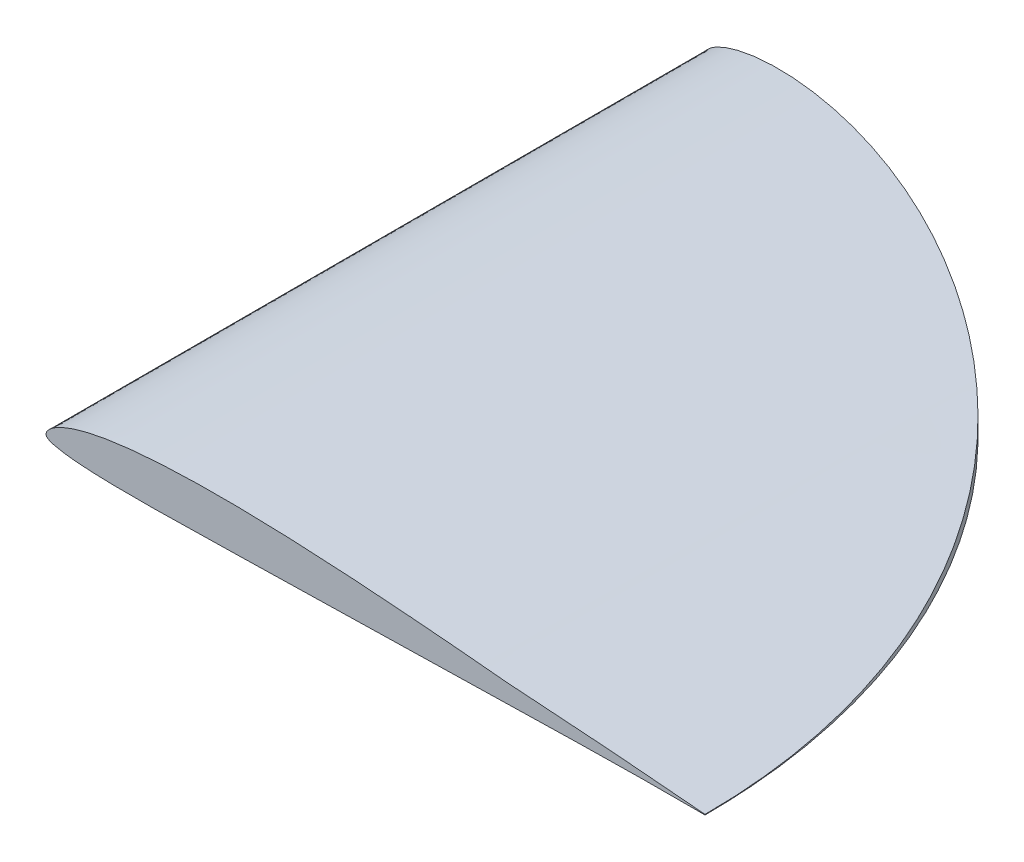
SolidWorks part; units mm, degrees
ref_plane "Front Plane" through (0, 0, 0) normal (0, 0, 1) x (1, 0, 0)
ref_plane "Top Plane" through (0, 0, 0) normal (0, 1, 0) x (1, 0, 0)
ref_plane "Right Plane" through (0, 0, 0) normal (1, 0, 0) x (0, 0, -1)
curve "Curve1"
  spline degree 3 poles (25.4, 0.0107, 0) (25.3506, 0.0152, 0) (25.2009, 0.0289, 0) (24.9376, 0.0531, 0) (24.6076, 0.082, 0) (24.2616, 0.1124, 0) (23.9125, 0.1431, 0) (23.5625, 0.1725, 0) (23.212, 0.2019, 0) (22.8613, 0.2307, 0) (22.5105, 0.2591, 0) (22.1596, 0.2869, 0) (21.8089, 0.314, 0) (21.4582, 0.3409, 0) (21.1077, 0.367, 0) (20.7573, 0.3928, 0) (20.407, 0.4182, 0) (20.0568, 0.4428, 0) (19.7068, 0.4673, 0) (19.3568, 0.4911, 0) (19.0069, 0.5145, 0) (18.6571, 0.5374, 0) (18.3335, 0.5583, 0) (18.0818, 0.5739, 0) (17.9246, 0.5843, 0) (17.8356, 0.5888, 0) (17.7472, 0.5983, 0) (17.5613, 0.6156, 0) (17.278, 0.6431, 0) (16.98, 0.6709, 0) (16.7137, 0.6956, 0) (16.4751, 0.7176, 0) (16.176, 0.7447, 0) (15.8267, 0.776, 0) (15.4701, 0.8073, 0) (15.1145, 0.838, 0) (14.7793, 0.8663, 0) (14.4495, 0.8936, 0) (14.1621, 0.9169, 0) (13.925, 0.9358, 0) (13.6642, 0.9563, 0) (13.3619, 0.9794, 0) (13.0103, 1.0056, 0) (12.659, 1.031, 0) (12.3077, 1.0554, 0) (11.9565, 1.0789, 0) (11.6054, 1.1014, 0) (11.2544, 1.1228, 0) (10.9034, 1.1432, 0) (10.5525, 1.1624, 0) (10.2016, 1.1803, 0) (9.8507, 1.197, 0) (9.5, 1.2123, 0) (9.1492, 1.2263, 0) (8.7986, 1.2386, 0) (8.448, 1.2494, 0) (8.0977, 1.2585, 0) (7.7474, 1.2658, 0) (7.3974, 1.2711, 0) (7.0475, 1.2745, 0) (6.6979, 1.2756, 0) (6.3485, 1.2744, 0) (5.9995, 1.2706, 0) (5.6509, 1.2642, 0) (5.3028, 1.2548, 0) (4.9554, 1.2422, 0) (4.6087, 1.2261, 0) (4.2629, 1.2062, 0) (3.9183, 1.1823, 0) (3.5751, 1.1536, 0) (3.2336, 1.12, 0) (2.8944, 1.0807, 0) (2.5581, 1.0351, 0) (2.2254, 0.9824, 0) (1.8975, 0.9214, 0) (1.5762, 0.8511, 0) (1.2643, 0.7698, 0) (0.9677, 0.6771, 0) (0.6972, 0.5737, 0) (0.4689, 0.4653, 0) (0.2948, 0.361, 0) (0.1747, 0.2696, 0) (0.0967, 0.1939, 0) (0.0471, 0.1311, 0) (0.0171, 0.0777, 0) (0.0019, 0.0319, 0) (-0.0016, -0.0085, 0) (0.0071, -0.0466, 0) (0.0322, -0.0832, 0) (0.0764, -0.1158, 0) (0.1405, -0.1489, 0) (0.2348, -0.1846, 0) (0.3747, -0.2244, 0) (0.5727, -0.265, 0) (0.8268, -0.3029, 0) (1.1218, -0.3343, 0) (1.4394, -0.3584, 0) (1.7684, -0.3763, 0) (2.1036, -0.389, 0) (2.4428, -0.3976, 0) (2.7846, -0.4031, 0) (3.1285, -0.4061, 0) (3.4739, -0.407, 0) (3.8205, -0.4061, 0) (4.168, -0.4035, 0) (4.5164, -0.3997, 0) (4.8654, -0.3948, 0) (5.2151, -0.389, 0) (5.5654, -0.3825, 0) (5.9165, -0.3755, 0) (6.2684, -0.368, 0) (6.621, -0.3604, 0) (6.9745, -0.3524, 0) (7.3287, -0.3442, 0) (7.6835, -0.336, 0) (8.039, -0.3276, 0) (8.3948, -0.3192, 0) (8.7511, -0.3108, 0) (9.1077, -0.3024, 0) (9.4646, -0.2939, 0) (9.8219, -0.2855, 0) (10.1795, -0.2771, 0) (10.5373, -0.2687, 0) (10.8952, -0.2603, 0) (11.2527, -0.252, 0) (11.6101, -0.2438, 0) (11.9672, -0.2355, 0) (12.3241, -0.2274, 0) (12.6807, -0.2193, 0) (13.0371, -0.2114, 0) (13.3934, -0.2033, 0) (13.6949, -0.1966, 0) (13.9592, -0.1908, 0) (14.1921, -0.1856, 0) (14.4749, -0.1792, 0) (14.7878, -0.1723, 0) (15.131, -0.1647, 0) (15.4754, -0.1569, 0) (15.8234, -0.1492, 0) (16.1349, -0.1423, 0) (16.4075, -0.1363, 0) (16.6379, -0.1313, 0) (16.9029, -0.1255, 0) (17.2072, -0.1189, 0) (17.4885, -0.1128, 0) (17.6791, -0.1088, 0) (17.7715, -0.1068, 0) (17.8501, -0.1053, 0) (18.0096, -0.1018, 0) (18.269, -0.0964, 0) (18.61, -0.0893, 0) (18.9621, -0.082, 0) (19.3141, -0.0749, 0) (19.666, -0.0678, 0) (20.0179, -0.0609, 0) (20.3698, -0.054, 0) (20.7219, -0.0473, 0) (21.074, -0.0408, 0) (21.4262, -0.0348, 0) (21.7784, -0.0292, 0) (22.1308, -0.0242, 0) (22.4832, -0.0197, 0) (22.8357, -0.0157, 0) (23.1883, -0.0125, 0) (23.5408, -0.0098, 0) (23.8935, -0.008, 0) (24.246, -0.0071, 0) (24.5963, -0.007, 0) (24.9308, -0.0084, 0) (25.198, -0.0096, 0) (25.3499, -0.0104, 0) (25.4, -0.0107, 0) knots 0 0 0 0 0.002901 0.008799 0.015478 0.022288 0.029131 0.035985 0.042847 0.049714 0.056581 0.063448 0.070313 0.077171 0.084031 0.090885 0.097737 0.104584 0.111432 0.118275 0.125116 0.131954 0.138793 0.144098 0.146709 0.148014 0.149313 0.151911 0.158945 0.165974 0.169425 0.174599 0.18 0.186998 0.195126 0.200949 0.20789 0.214818 0.220317 0.224762 0.228741 0.235631 0.242503 0.249376 0.256249 0.263115 0.269975 0.276837 0.283698 0.290553 0.297409 0.304262 0.311112 0.317958 0.324805 0.331647 0.338484 0.345319 0.352149 0.358974 0.365797 0.372613 0.37942 0.386225 0.393018 0.399801 0.406576 0.413331 0.420073 0.426793 0.433487 0.440154 0.446776 0.453353 0.459862 0.466294 0.472602 0.478718 0.484477 0.489534 0.493496 0.496331 0.498346 0.499841 0.500999 0.501915 0.502649 0.503345 0.504158 0.505185 0.506526 0.508376 0.511074 0.515031 0.520197 0.526109 0.532386 0.538838 0.545393 0.552019 0.558693 0.565404 0.572145 0.578909 0.585689 0.592488 0.599298 0.60612 0.612956 0.619809 0.626673 0.633554 0.640451 0.647364 0.654291 0.661227 0.668172 0.675126 0.682086 0.689049 0.69602 0.703 0.709987 0.71697 0.723948 0.73092 0.73789 0.744856 0.751814 0.758769 0.765721 0.77267 0.776424 0.78119 0.786305 0.792978 0.79951 0.806399 0.81314 0.819881 0.824633 0.829103 0.833367 0.840145 0.84692 0.849831 0.851305 0.852333 0.85443 0.860642 0.867519 0.87439 0.881257 0.888123 0.894989 0.901857 0.908727 0.915597 0.922469 0.929344 0.936217 0.943092 0.949972 0.956848 0.963729 0.970609 0.97749 0.984361 0.991109 0.997067 1 1 1 1
sketch "Sketch2" plane through (0, 0, 0) normal (0, 0, 1) x (1, 0, 0)
  line L0 (64.7182, -2.4991) -> (64.7182, -2.5635)
  line L1 (127, 0.0536) -> (127, -0.0536)
  line L2 (25.4, 0.0107) -> (25.4, -0.0107)
  line L3 (279.4, 0.1179) -> (279.4, -0.1179)
  line L4 (609.6, 0.2573) -> (609.6, -0.2573)
  spline S1 degree 3 poles (609.6, 0.2573) (608.4153, 0.3652) (604.8219, 0.6927) (598.502, 1.2752) (590.5825, 1.9674) (582.2775, 2.6983) (573.9006, 3.4339) (565.4998, 4.1403) (557.089, 4.8463) (548.6715, 5.5358) (540.2515, 6.218) (531.8311, 6.8852) (523.413, 7.5348) (514.9974, 8.1818) (506.5852, 8.8084) (498.1747, 9.4281) (489.7686, 10.036) (481.3637, 10.627) (472.9627, 11.2149) (464.5629, 11.7866) (456.1664, 12.3471) (447.7708, 12.8983) (440.0032, 13.3997) (433.9644, 13.7741) (430.1915, 14.0231) (428.0555, 14.1319) (425.9338, 14.3593) (421.4712, 14.7735) (414.6712, 15.4343) (407.5204, 16.1015) (401.1285, 16.6942) (395.4014, 17.222) (388.2248, 17.8734) (379.8411, 18.6251) (371.2834, 19.3759) (362.7481, 20.1109) (354.702, 20.791) (346.7874, 21.4473) (339.8916, 22.0057) (334.2002, 22.4585) (327.9397, 22.9514) (320.686, 23.506) (312.248, 24.1341) (303.8155, 24.7432) (292.5775, 25.5244) (281.3407, 26.2607) (270.1062, 26.9482) (261.6823, 27.4364) (250.4535, 28.0507) (239.2258, 28.6059) (227.9988, 29.096) (219.5815, 29.4314) (211.1661, 29.7272) (202.7531, 29.9856) (194.3438, 30.2035) (185.9386, 30.3795) (177.5376, 30.5072) (169.1408, 30.5885) (160.7491, 30.6149) (152.3646, 30.5852) (143.9885, 30.4949) (135.6226, 30.341) (127.2682, 30.115) (118.9286, 29.8125) (110.6079, 29.4273) (102.3088, 28.9496) (94.0382, 28.3746) (85.8017, 27.6874) (77.6067, 26.8808) (69.4667, 25.9361) (61.3935, 24.8424) (53.4108, 23.5771) (45.5411, 22.1146) (37.8288, 20.426) (30.344, 18.4761) (23.2242, 16.2498) (16.7336, 13.7685) (11.2526, 11.1662) (7.0744, 8.6642) (4.192, 6.4716) (2.3207, 4.6541) (1.1306, 3.147) (0.4097, 1.8653) (0.0445, 0.7644) (-0.0394, -0.2051) (0.1701, -1.1192) (0.7717, -1.9972) (1.8329, -2.7786) (3.3717, -3.5735) (5.6341, -4.4311) (8.992, -5.3852) (13.7441, -6.3602) (19.844, -7.2691) (26.9221, -8.0223) (34.5451, -8.6019) (42.4418, -9.0313) (50.4869, -9.3361) (58.6261, -9.543) (66.8307, -9.6749) (75.0831, -9.7467) (83.3728, -9.7692) (91.6908, -9.7458) (100.0329, -9.6848) (108.3931, -9.5935) (116.7701, -9.4746) (125.1618, -9.3356) (133.5708, -9.1799) (141.9971, -9.0125) (150.4416, -8.8321) (158.9043, -8.6491) (167.3869, -8.4567) (175.8879, -8.2608) (187.2521, -7.9967) (198.6327, -7.7272) (210.0269, -7.4583) (218.5851, -7.2569) (227.1506, -7.0539) (235.7244, -6.8527) (244.3077, -6.6496) (252.896, -6.449) (261.4836, -6.2483) (270.0654, -6.0486) (278.6417, -5.8521) (287.2128, -5.6526) (295.7783, -5.4585) (304.3375, -5.264) (312.891, -5.0728) (321.4408, -4.88) (328.6786, -4.7192) (337.1174, -4.5324) (345.4426, -4.3447) (354.9071, -4.135) (363.1446, -3.9522) (371.4102, -3.7664) (379.7615, -3.5814) (387.2366, -3.4158) (393.7811, -3.2715) (399.3097, -3.1512) (405.6693, -3.0117) (412.9735, -2.8543) (419.723, -2.7081) (424.2983, -2.6117) (426.5172, -2.5634) (428.4027, -2.5274) (432.2303, -2.443) (438.4564, -2.3133) (446.6397, -2.1424) (455.0912, -1.9684) (463.5382, -1.7984) (471.983, -1.6281) (480.4288, -1.4625) (488.876, -1.2962) (497.3253, -1.1358) (505.7757, -0.9782) (514.2284, -0.8363) (525.5014, -0.6571) (536.7782, -0.5043) (548.0561, -0.376) (556.518, -0.299) (564.9803, -0.2347) (573.4446, -0.1921) (581.9048, -0.1708) (590.3111, -0.1673) (598.3385, -0.2004) (604.7515, -0.2296) (608.3973, -0.2504) (609.6, -0.2573) knots 0 0 0 0 0.002901 0.008799 0.015478 0.022288 0.029131 0.035985 0.042847 0.049714 0.056581 0.063448 0.070313 0.077171 0.084031 0.090885 0.097737 0.104584 0.111432 0.118275 0.125116 0.131954 0.138793 0.144098 0.146709 0.148014 0.149313 0.151911 0.158945 0.165974 0.169425 0.174599 0.18 0.186998 0.195126 0.200949 0.20789 0.214818 0.220317 0.224762 0.228741 0.235631 0.242503 0.249376 0.256249 0.269975 0.276837 0.283698 0.290553 0.304262 0.311112 0.317958 0.324805 0.331647 0.338484 0.345319 0.352149 0.358974 0.365797 0.372613 0.37942 0.386225 0.393018 0.399801 0.406576 0.413331 0.420073 0.426793 0.433487 0.440154 0.446776 0.453353 0.459862 0.466294 0.472602 0.478718 0.484477 0.489534 0.493496 0.496331 0.498346 0.499841 0.500999 0.501915 0.502649 0.503345 0.504158 0.505185 0.506526 0.508376 0.511074 0.515031 0.520197 0.526109 0.532386 0.538838 0.545393 0.552019 0.558693 0.565404 0.572145 0.578909 0.585689 0.592488 0.599298 0.60612 0.612956 0.619809 0.626673 0.633554 0.640451 0.647364 0.654291 0.668172 0.675126 0.682086 0.689049 0.69602 0.703 0.709987 0.71697 0.723948 0.73092 0.73789 0.744856 0.751814 0.758769 0.765721 0.77267 0.776424 0.786305 0.792978 0.79951 0.806399 0.81314 0.819881 0.824633 0.829103 0.833367 0.840145 0.84692 0.849831 0.851305 0.852333 0.85443 0.860642 0.867519 0.87439 0.881257 0.888123 0.894989 0.901857 0.908727 0.915597 0.922469 0.929344 0.943092 0.949972 0.956848 0.963729 0.970609 0.97749 0.984361 0.991109 0.997067 1 1 1 1
  spline S2 degree 3 poles (127, 0.0536) (126.7532, 0.0761) (126.0046, 0.1443) (124.6879, 0.2657) (123.038, 0.4099) (121.3078, 0.5622) (119.5626, 0.7154) (117.8125, 0.8626) (116.0602, 1.0096) (114.3066, 1.1533) (112.5524, 1.2954) (110.7981, 1.4344) (109.0444, 1.5698) (107.2911, 1.7045) (105.5386, 1.8351) (103.7864, 1.9642) (102.0351, 2.0908) (100.2841, 2.214) (98.5339, 2.3364) (96.7839, 2.4555) (95.0347, 2.5723) (93.2856, 2.6871) (91.6673, 2.7916) (90.4092, 2.8696) (89.6232, 2.9215) (89.1782, 2.9441) (88.7362, 2.9915) (87.8065, 3.0778) (86.3898, 3.2155) (84.9001, 3.3545) (83.5684, 3.478) (82.3753, 3.5879) (80.8802, 3.7236) (79.1336, 3.8802) (77.3507, 4.0366) (75.5725, 4.1898) (73.8963, 4.3315) (72.2474, 4.4682) (70.8107, 4.5845) (69.625, 4.6789) (68.3208, 4.7815) (66.8096, 4.8971) (65.0517, 5.0279) (63.2949, 5.1548) (60.9536, 5.3176) (58.6126, 5.471) (56.2721, 5.6142) (54.5172, 5.7159) (52.1778, 5.8439) (49.8387, 5.9596) (47.4998, 6.0617) (45.7461, 6.1315) (43.9929, 6.1932) (42.2402, 6.247) (40.4883, 6.2924) (38.7372, 6.3291) (36.987, 6.3557) (35.2377, 6.3726) (33.4894, 6.3781) (31.7426, 6.3719) (29.9976, 6.3531) (28.2547, 6.321) (26.5142, 6.274) (24.7768, 6.2109) (23.0433, 6.1307) (21.3143, 6.0312) (19.5913, 5.9114) (17.8753, 5.7682) (16.1681, 5.6002) (14.4722, 5.4034) (12.7903, 5.1755) (11.1272, 4.9119) (9.4877, 4.6072) (7.881, 4.2554) (6.3217, 3.8492) (4.8384, 3.3854) (3.4862, 2.8684) (2.3443, 2.3263) (1.4738, 1.805) (0.8733, 1.3482) (0.4835, 0.9696) (0.2355, 0.6556) (0.0854, 0.3886) (0.0093, 0.1593) (-0.0082, -0.0427) (0.0354, -0.2332) (0.1608, -0.4161) (0.3818, -0.5789) (0.7024, -0.7445) (1.1738, -0.9231) (1.8733, -1.1219) (2.8634, -1.3251) (4.1342, -1.5144) (5.6088, -1.6713) (7.1969, -1.7921) (8.842, -1.8815) (10.5181, -1.945) (12.2138, -1.9881) (13.9231, -2.0156) (15.6423, -2.0306) (17.3693, -2.0352) (19.1023, -2.0304) (20.8402, -2.0177) (22.5819, -1.9987) (24.3271, -1.9739) (26.0754, -1.9449) (27.8272, -1.9125) (29.5827, -1.8776) (31.342, -1.84) (33.1051, -1.8019) (34.8723, -1.7618) (36.6433, -1.721) (39.0109, -1.666) (41.3818, -1.6098) (43.7556, -1.5538) (45.5386, -1.5118) (47.323, -1.4696) (49.1093, -1.4276) (50.8974, -1.3853) (52.6867, -1.3435) (54.4758, -1.3017) (56.2636, -1.2601) (58.0503, -1.2192) (59.836, -1.1776) (61.6205, -1.1372) (63.4036, -1.0967) (65.1856, -1.0568) (66.9668, -1.0167) (68.4747, -0.9832) (70.2328, -0.9443) (71.9672, -0.9051) (73.939, -0.8615) (75.6551, -0.8234) (77.3771, -0.7847) (79.117, -0.7461) (80.6743, -0.7116) (82.0377, -0.6816) (83.1895, -0.6565) (84.5144, -0.6274) (86.0361, -0.5947) (87.4423, -0.5642) (88.3955, -0.5441) (88.8577, -0.534) (89.2506, -0.5265) (90.048, -0.509) (91.3451, -0.4819) (93.0499, -0.4463) (94.8107, -0.4101) (96.5705, -0.3747) (98.3298, -0.3392) (100.0893, -0.3047) (101.8492, -0.27) (103.6094, -0.2366) (105.3699, -0.2038) (107.1309, -0.1742) (109.4795, -0.1369) (111.8288, -0.1051) (114.1784, -0.0783) (115.9413, -0.0623) (117.7042, -0.0489) (119.4676, -0.04) (121.2302, -0.0356) (122.9815, -0.0349) (124.6538, -0.0418) (125.9899, -0.0478) (126.7494, -0.0522) (127, -0.0536) knots 0 0 0 0 0.002901 0.008799 0.015478 0.022288 0.029131 0.035985 0.042847 0.049714 0.056581 0.063448 0.070313 0.077171 0.084031 0.090885 0.097737 0.104584 0.111432 0.118275 0.125116 0.131954 0.138793 0.144098 0.146709 0.148014 0.149313 0.151911 0.158945 0.165974 0.169425 0.174599 0.18 0.186998 0.195126 0.200949 0.20789 0.214818 0.220317 0.224762 0.228741 0.235631 0.242503 0.249376 0.256249 0.269975 0.276837 0.283698 0.290553 0.304262 0.311112 0.317958 0.324805 0.331647 0.338484 0.345319 0.352149 0.358974 0.365797 0.372613 0.37942 0.386225 0.393018 0.399801 0.406576 0.413331 0.420073 0.426793 0.433487 0.440154 0.446776 0.453353 0.459862 0.466294 0.472602 0.478718 0.484477 0.489534 0.493496 0.496331 0.498346 0.499841 0.500999 0.501915 0.502649 0.503345 0.504158 0.505185 0.506526 0.508376 0.511074 0.515031 0.520197 0.526109 0.532386 0.538838 0.545393 0.552019 0.558693 0.565404 0.572145 0.578909 0.585689 0.592488 0.599298 0.60612 0.612956 0.619809 0.626673 0.633554 0.640451 0.647364 0.654291 0.668172 0.675126 0.682086 0.689049 0.69602 0.703 0.709987 0.71697 0.723948 0.73092 0.73789 0.744856 0.751814 0.758769 0.765721 0.77267 0.776424 0.786305 0.792978 0.79951 0.806399 0.81314 0.819881 0.824633 0.829103 0.833367 0.840145 0.84692 0.849831 0.851305 0.852333 0.85443 0.860642 0.867519 0.87439 0.881257 0.888123 0.894989 0.901857 0.908727 0.915597 0.922469 0.929344 0.943092 0.949972 0.956848 0.963729 0.970609 0.97749 0.984361 0.991109 0.997067 1 1 1 1
  spline S3 degree 3 poles (279.4, 0.1179) (278.857, 0.1674) (277.21, 0.3175) (274.3134, 0.5845) (270.6837, 0.9017) (266.8772, 1.2367) (263.0378, 1.5739) (259.1874, 1.8976) (255.3325, 2.2212) (251.4744, 2.5372) (247.6153, 2.8499) (243.7559, 3.1557) (239.8976, 3.4535) (236.0405, 3.75) (232.1849, 4.0372) (228.3301, 4.3212) (224.4773, 4.5998) (220.625, 4.8707) (216.7746, 5.1402) (212.9247, 5.4022) (209.0763, 5.6591) (205.2283, 5.9117) (201.6681, 6.1415) (198.9003, 6.3131) (197.1711, 6.4272) (196.1921, 6.4771) (195.2197, 6.5813) (193.1743, 6.7712) (190.0576, 7.0741) (186.7802, 7.3798) (183.8506, 7.6515) (181.2256, 7.8934) (177.9364, 8.192) (174.0938, 8.5365) (170.1716, 8.8806) (166.2595, 9.2175) (162.5718, 9.5292) (158.9442, 9.83) (155.7836, 10.086) (153.1751, 10.2935) (150.3057, 10.5194) (146.9811, 10.7736) (143.1137, 11.0615) (139.2488, 11.3406) (134.098, 11.6987) (128.9478, 12.0362) (123.7987, 12.3513) (119.9377, 12.575) (114.7912, 12.8566) (109.6452, 13.111) (104.4995, 13.3357) (100.6415, 13.4894) (96.7844, 13.625) (92.9285, 13.7434) (89.0743, 13.8433) (85.2219, 13.9239) (81.3714, 13.9825) (77.5229, 14.0197) (73.6767, 14.0318) (69.8338, 14.0182) (65.9947, 13.9768) (62.1604, 13.9063) (58.3313, 13.8027) (54.5089, 13.6641) (50.6953, 13.4875) (46.8916, 13.2686) (43.1009, 13.005) (39.3258, 12.6901) (35.5697, 12.3204) (31.8389, 11.8874) (28.1387, 11.3861) (24.4799, 10.8062) (20.873, 10.1358) (17.3382, 9.3619) (13.9077, 8.4682) (10.6444, 7.4478) (7.6696, 6.3105) (5.1574, 5.1178) (3.2424, 3.9711) (1.9213, 2.9661) (1.0637, 2.1331) (0.5182, 1.4424) (0.1878, 0.8549) (0.0204, 0.3504) (-0.0181, -0.094) (0.078, -0.513) (0.3537, -0.9154) (0.8401, -1.2735) (1.5454, -1.6379) (2.5823, -2.0309) (4.1213, -2.4682) (6.2994, -2.9151) (9.0952, -3.3317) (12.3393, -3.6769) (15.8332, -3.9425) (19.4525, -4.1394) (23.1398, -4.279) (26.8703, -4.3739) (30.6307, -4.4343) (34.4131, -4.4672) (38.2125, -4.4775) (42.025, -4.4668) (45.8484, -4.4389) (49.6802, -4.397) (53.5196, -4.3425) (57.3658, -4.2788) (61.2199, -4.2075) (65.082, -4.1307) (68.9524, -4.048) (72.8311, -3.9642) (76.719, -3.876) (80.6153, -3.7862) (85.8239, -3.6652) (91.04, -3.5416) (96.2623, -3.4184) (100.1848, -3.3261) (104.1107, -3.233) (108.0404, -3.1408) (111.9744, -3.0478) (115.9107, -2.9558) (119.8467, -2.8638) (123.78, -2.7723) (127.7108, -2.6822) (131.6392, -2.5908) (135.5651, -2.5018) (139.488, -2.4127) (143.4084, -2.325) (147.3271, -2.2367) (150.6444, -2.163) (154.5121, -2.0774) (158.3279, -1.9913) (162.6657, -1.8952) (166.4413, -1.8114) (170.2297, -1.7263) (174.0574, -1.6415) (177.4834, -1.5656) (180.483, -1.4995) (183.017, -1.4443) (185.9318, -1.3804) (189.2795, -1.3082) (192.373, -1.2412) (194.47, -1.197) (195.487, -1.1749) (196.3513, -1.1584) (198.1056, -1.1197) (200.9592, -1.0603) (204.7098, -0.9819) (208.5834, -0.9022) (212.455, -0.8243) (216.3255, -0.7462) (220.1965, -0.6703) (224.0682, -0.5941) (227.9407, -0.5206) (231.8138, -0.4484) (235.688, -0.3833) (240.8548, -0.3012) (246.0233, -0.2311) (251.1924, -0.1723) (255.0708, -0.1371) (258.9493, -0.1076) (262.8288, -0.0881) (266.7064, -0.0783) (270.5592, -0.0767) (274.2385, -0.0919) (277.1778, -0.1052) (278.8487, -0.1148) (279.4, -0.1179) knots 0 0 0 0 0.002901 0.008799 0.015478 0.022288 0.029131 0.035985 0.042847 0.049714 0.056581 0.063448 0.070313 0.077171 0.084031 0.090885 0.097737 0.104584 0.111432 0.118275 0.125116 0.131954 0.138793 0.144098 0.146709 0.148014 0.149313 0.151911 0.158945 0.165974 0.169425 0.174599 0.18 0.186998 0.195126 0.200949 0.20789 0.214818 0.220317 0.224762 0.228741 0.235631 0.242503 0.249376 0.256249 0.269975 0.276837 0.283698 0.290553 0.304262 0.311112 0.317958 0.324805 0.331647 0.338484 0.345319 0.352149 0.358974 0.365797 0.372613 0.37942 0.386225 0.393018 0.399801 0.406576 0.413331 0.420073 0.426793 0.433487 0.440154 0.446776 0.453353 0.459862 0.466294 0.472602 0.478718 0.484477 0.489534 0.493496 0.496331 0.498346 0.499841 0.500999 0.501915 0.502649 0.503345 0.504158 0.505185 0.506526 0.508376 0.511074 0.515031 0.520197 0.526109 0.532386 0.538838 0.545393 0.552019 0.558693 0.565404 0.572145 0.578909 0.585689 0.592488 0.599298 0.60612 0.612956 0.619809 0.626673 0.633554 0.640451 0.647364 0.654291 0.668172 0.675126 0.682086 0.689049 0.69602 0.703 0.709987 0.71697 0.723948 0.73092 0.73789 0.744856 0.751814 0.758769 0.765721 0.77267 0.776424 0.786305 0.792978 0.79951 0.806399 0.81314 0.819881 0.824633 0.829103 0.833367 0.840145 0.84692 0.849831 0.851305 0.852333 0.85443 0.860642 0.867519 0.87439 0.881257 0.888123 0.894989 0.901857 0.908727 0.915597 0.922469 0.929344 0.943092 0.949972 0.956848 0.963729 0.970609 0.97749 0.984361 0.991109 0.997067 1 1 1 1
extrude "Boss-Extrude1" add sketch "Sketch2" against normal blind 609.6
sketch "Sketch3" plane through (0, 0, 0) normal (0, 1, 0) x (1, 0, 0)
  line L1 (0, 0) -> (609.6, 0)
  line L2 (0, 0) -> (0, 609.6)
  line L3 (0, 609.6) -> (609.6, 609.6)
  line L4 (609.6, 0) -> (609.6, 609.6)
  arc A0 (609.6, 0) -> (0, 609.6) centre (0, 0) ccw
  dimension "D1" = 609.6
extrude "Cut-Extrude1" cut sketch "Sketch3" against normal through all both and the other way through all contours A0 L4 L3
